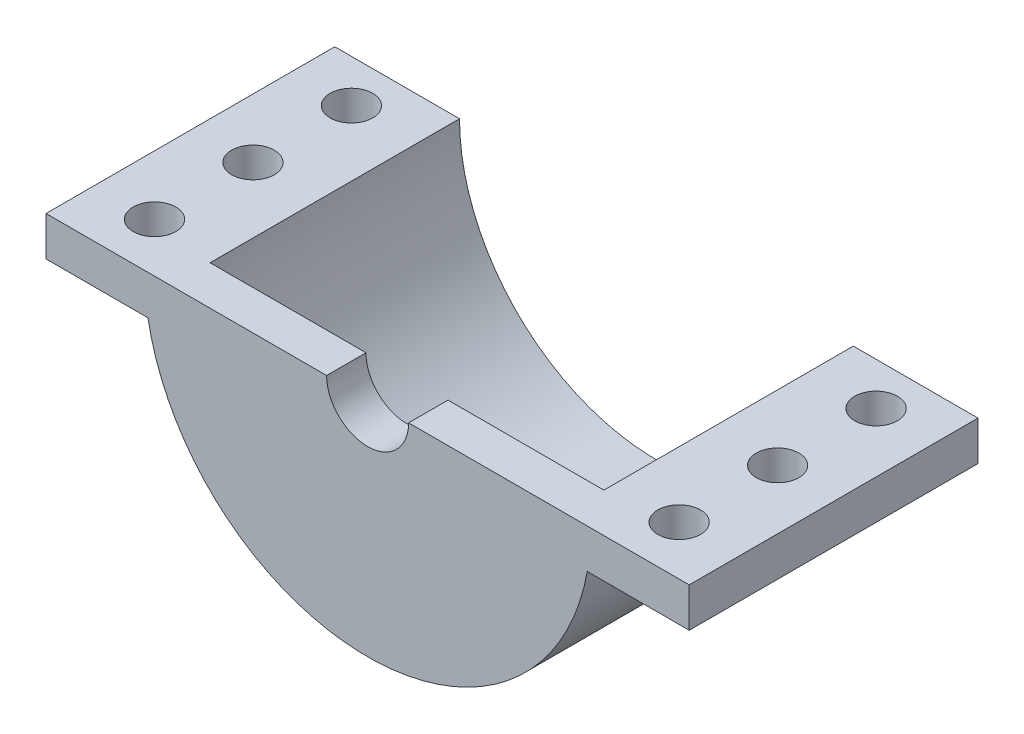
SolidWorks part; units mm, degrees
ref_plane "Alzado" through (0, 0, 0) normal (0, 0, 1) x (1, 0, 0)
ref_plane "Planta" through (0, 0, 0) normal (0, 1, 0) x (1, 0, 0)
ref_plane "Vista lateral" through (0, 0, 0) normal (1, 0, 0) x (0, 0, -1)
sketch "Croquis1" plane through (0, 0, 0) normal (0, 0, 1) x (1, 0, 0)
  line L0 (-17, 0) -> (17, 0)
  circle A0 centre (0, 0) radius 15
  circle A1 centre (0, 0) radius 17
  dimension "D1" = 2
  dimension "D2" = 30
extrude "Saliente-Extruir1" add sketch "Croquis1" along normal blind 19 contours L0 A1 A0
sketch "Croquis2" plane through (0, 0, 19) normal (0, 0, 1) x (1, 0, 0)
  line L0 (-17, 0) -> (17, 0)
  arc A0 (-17, 0) -> (17, 0) centre (0, 0) ccw construction
  circle A1 centre (0, 0) radius 17
  line M1 (-15, 0) -> (-17, 0)
  arc M2 (-17, 0) -> (17, 0) centre (0, 0) ccw
  line M3 (17, 0) -> (15, 0)
  arc M4 (15, 0) -> (-15, 0) centre (0, 0) cw
extrude "Saliente-Extruir2" add sketch "Croquis2" along normal blind 3 contours L0 M4 | M4 M1 M2 M3
sketch "Croquis3" plane through (0, 0, 22) normal (0, 0, 1) x (1, 0, 0)
  circle A0 centre (0, 0) radius 3.125
  dimension "D1" = 6.25
extrude "Cortar-Extruir1" cut sketch "Croquis3" against normal blind 3
sketch "Croquis4" plane through (0, 0, 22) normal (0, 0, 1) x (1, 0, 0)
  line L0 (-17, 0) -> (-3.125, 0) construction
  line L1 (-16.7332, 0) -> (-24.5, 0)
  line L2 (-16.7332, 0) -> (-16.7332, -3)
  line L3 (-16.7332, -3) -> (-24.5, -3)
  line L4 (-24.5, 0) -> (-24.5, -3)
  line L5 (0, 0) -> (0, 14.2852) construction
  line L6 (24.5, 0) -> (24.5, -3)
  line L7 (16.7332, -3) -> (24.5, -3)
  line L8 (16.7332, 0) -> (16.7332, -3)
  line L9 (16.7332, 0) -> (24.5, 0)
  arc A2 (-17, 0) -> (17, 0) centre (0, 0) ccw construction
  dimension "D1" = 3
  dimension "D2" = 7.5
extrude "Saliente-Extruir3" add sketch "Croquis4" against normal up to vertex (22 mm away) up to point (-17, 0, 0)
sketch "Croquis5" plane through (0, -3, 0) normal (0, -1, 0) x (1, 0, 0)
  line L0 (0, 0) -> (0, 14.2251) construction
  line L1 (-16.7332, 0) -> (16.7332, 0) construction
  line L2 (-16.7332, 0) -> (-16.7332, 22) construction
  line L3 (-24.5, 0) -> (-16.7332, 0) construction
  line L5 (-19.9832, 3.25) -> (-19.9832, 10.75) construction
  circle A0 centre (-19.9832, 3.25) radius 1.625
  circle A1 centre (-19.9832, 10.75) radius 1.625
  circle A2 centre (-19.9832, 18.25) radius 1.625
  circle A3 centre (19.9832, 18.25) radius 1.625
  circle A4 centre (19.9832, 10.75) radius 1.625
  circle A5 centre (19.9832, 3.25) radius 1.625
  dimension "D1" = 3.25
  dimension "D2" = 3.25
  dimension "D3" = 3.25
  dimension "D4" = 3
  dimension "D5" = 7.5
extrude "Cortar-Extruir2" cut sketch "Croquis5" against normal through all
